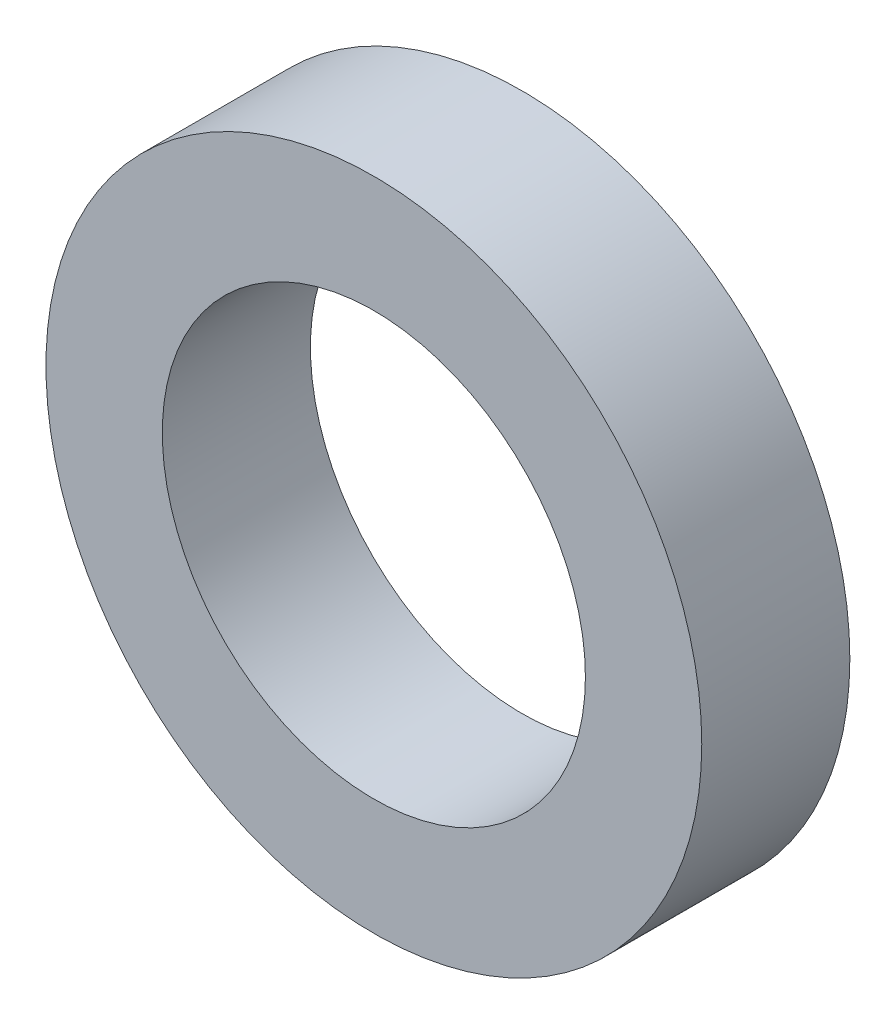
SolidWorks part; units mm, degrees
ref_plane "前视基准面" through (0, 0, 0) normal (0, 0, 1) x (1, 0, 0)
ref_plane "上视基准面" through (0, 0, 0) normal (0, 1, 0) x (1, 0, 0)
ref_plane "右视基准面" through (0, 0, 0) normal (1, 0, 0) x (0, 0, -1)
sketch "草图1" plane through (0, 0, 0) normal (0, 0, 1) x (1, 0, 0)
  circle A0 centre (0, 0) radius 7.75
  circle A1 centre (0, 0) radius 5
extrude "凸台-拉伸1" add sketch "草图1" against normal mid plane 3.5 contours A0
sketch "草图2" plane through (0, 0, 0) normal (0, 0, 1) x (1, 0, 0)
  circle A0 centre (0, 0) radius 5
extrude "切除-拉伸1" cut sketch "草图2" against normal mid plane 3.5
